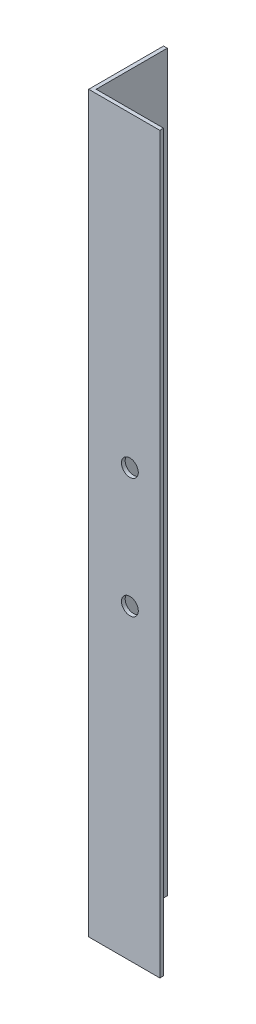
SolidWorks part; units mm, degrees
material "1060 Сплав"
ref_plane "Спереди" through (0, 0, 0) normal (0, 0, 1) x (1, 0, 0)
ref_plane "Сверху" through (0, 0, 0) normal (0, 1, 0) x (1, 0, 0)
ref_plane "Справа" through (0, 0, 0) normal (1, 0, 0) x (0, 0, -1)
sketch "Эскиз1" plane through (0, 0, 0) normal (0, 1, 0) x (1, 0, 0)
  line L0 (0, 0) -> (0, 20)
  line L1 (0, 20) -> (1, 20)
  line L2 (1, 20) -> (1, 1)
  line L3 (1, 1) -> (20, 1)
  line L4 (20, 1) -> (20, 0)
  line L5 (20, 0) -> (0, 0)
  dimension "D1" = 1
  dimension "D2" = 20
extrude "Бобышка-Вытянуть1" add sketch "Эскиз1" along normal blind 196
sketch "Эскиз2" plane through (20, 0, 0) normal (1, 0, 0) x (0, 0, -1)
  line L4 (0, 0) -> (1, 0)
  line L5 (1, 0) -> (1, 196)
  line L6 (1, 196) -> (0, 196)
  line L7 (0, 196) -> (0, 0)
  line L8 (0, 0) -> (1, 0)
  line L9 (1, 0) -> (1, 196)
  line L10 (1, 196) -> (0, 196)
  line L11 (0, 196) -> (0, 0)
  dimension "D1" = 0
extrude "Вырез-Вытянуть1" cut sketch "Эскиз2" against normal blind 1
sketch "Sketch1" plane through (0, 0, -1) normal (0, 0, -1) x (-1, 0, 0)
  circle A0 centre (-11, 82) radius 2.25 construction
  circle A1 centre (-11, 82) radius 2.25
  circle A2 centre (-11, 114) radius 2.25 construction
  circle A3 centre (-11, 114) radius 2.25
extrude "Cut-Extrude1" cut sketch "Sketch1" against normal through all
